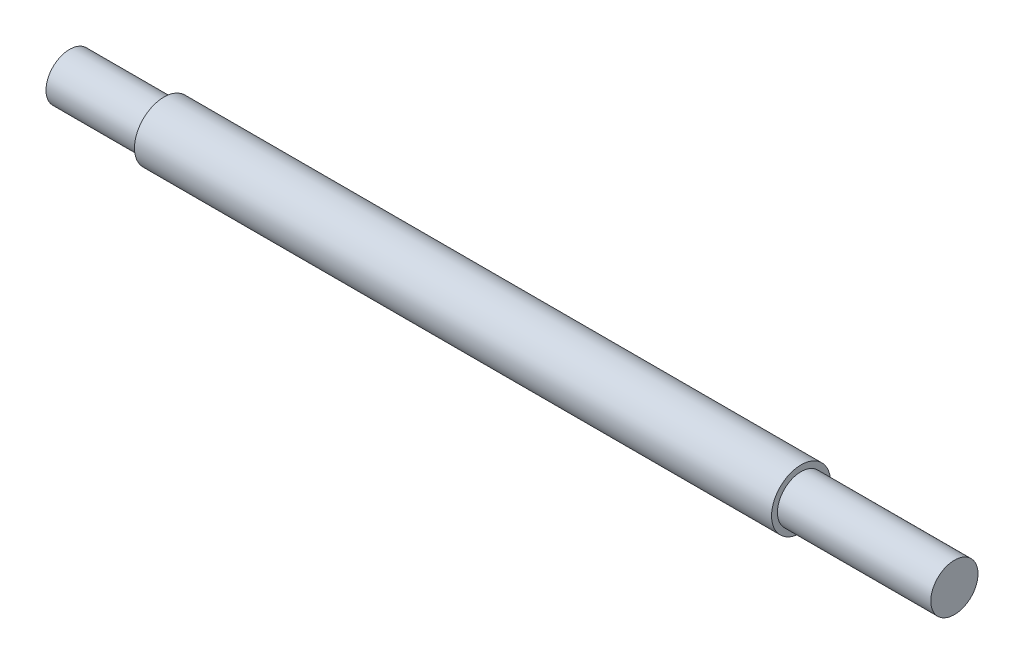
SolidWorks part; units mm, degrees
ref_plane "Front Plane" through (0, 0, 0) normal (0, 0, 1) x (1, 0, 0)
ref_plane "Top Plane" through (0, 0, 0) normal (0, 1, 0) x (1, 0, 0)
ref_plane "Right Plane" through (0, 0, 0) normal (1, 0, 0) x (0, 0, -1)
sketch "Sketch1" plane through (0, 0, 0) normal (1, 0, 0) x (0, 0, -1)
  circle A0 centre (0, 0) radius 2.5
  dimension "D1" = 5
extrude "Boss-Extrude1" add sketch "Sketch1" along normal mid plane 70
sketch "Sketch2" plane through (35, 0, 0) normal (1, 0, 0) x (0, 0, -1)
  circle A0 centre (0, 0) radius 2
  circle A1 centre (0, 0) radius 2.5
  dimension "D1" = 4
extrude "Cut-Extrude1" cut sketch "Sketch2" against normal blind 8
sketch "Sketch3" plane through (-35, 0, 0) normal (-1, 0, 0) x (0, 0, 1)
  circle A0 centre (0, 0) radius 2
  circle A1 centre (0, 0) radius 2.5
  dimension "D1" = 4
extrude "Cut-Extrude2" cut sketch "Sketch3" against normal blind 8
sketch "Sketch4" plane through (35, 0, 0) normal (1, 0, 0) x (0, 0, -1)
  circle A0 centre (0, 0) radius 2
extrude "Boss-Extrude2" add sketch "Sketch4" along normal blind 5 contours A0
